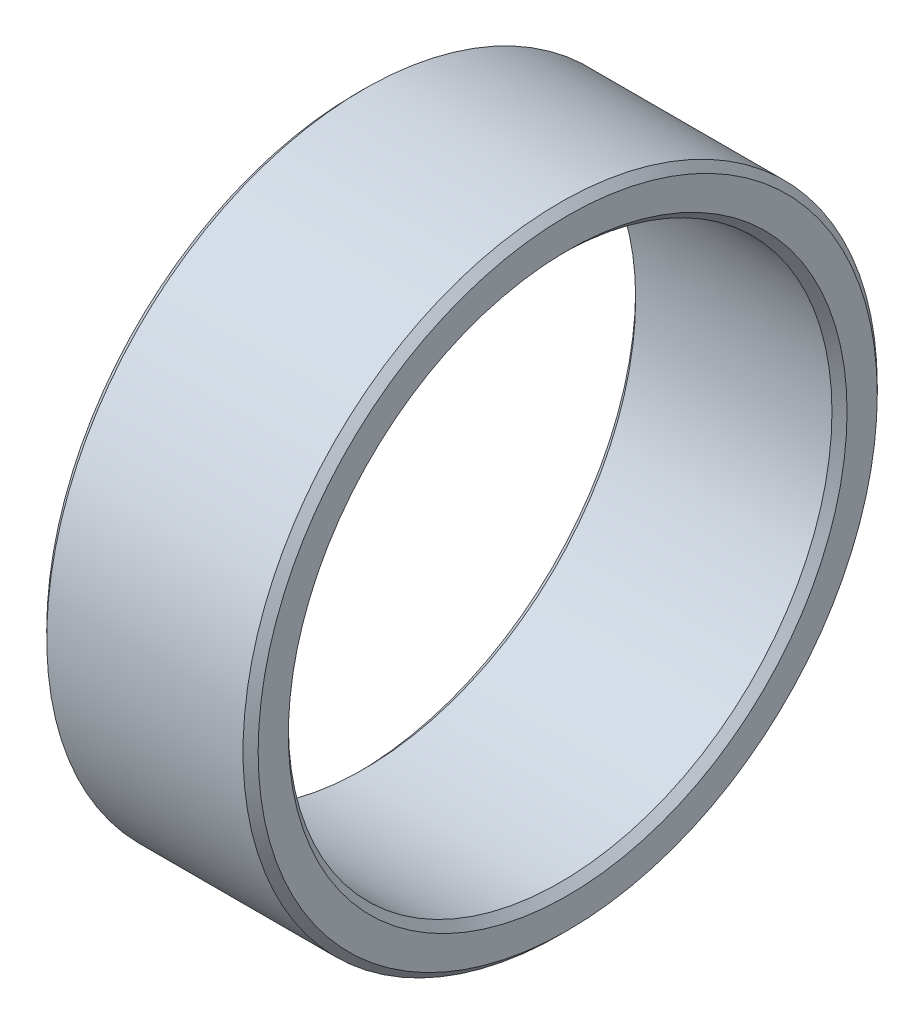
SolidWorks part; units mm, degrees
material "普通碳钢"
ref_plane "Front" through (0, 0, 0) normal (0, 0, 1) x (1, 0, 0)
ref_plane "Top" through (0, 0, 0) normal (0, 1, 0) x (1, 0, 0)
ref_plane "Right" through (0, 0, 0) normal (1, 0, 0) x (0, 0, -1)
sketch "草图1" plane through (0, 0, 0) normal (1, 0, 0) x (0, 0, -1)
  circle A0 centre (0, 0) radius 18
  circle A1 centre (0, 0) radius 21
  dimension "D1" = 36
  dimension "D2" = 3
extrude "凸台-拉伸1" add sketch "草图1" along normal blind 14
chamfer "倒角1" distance 0.5 angle 45 4 edges at (0, 0, -21) (0, 0, -18) (14, 0, -18) (14, 0, -21)
